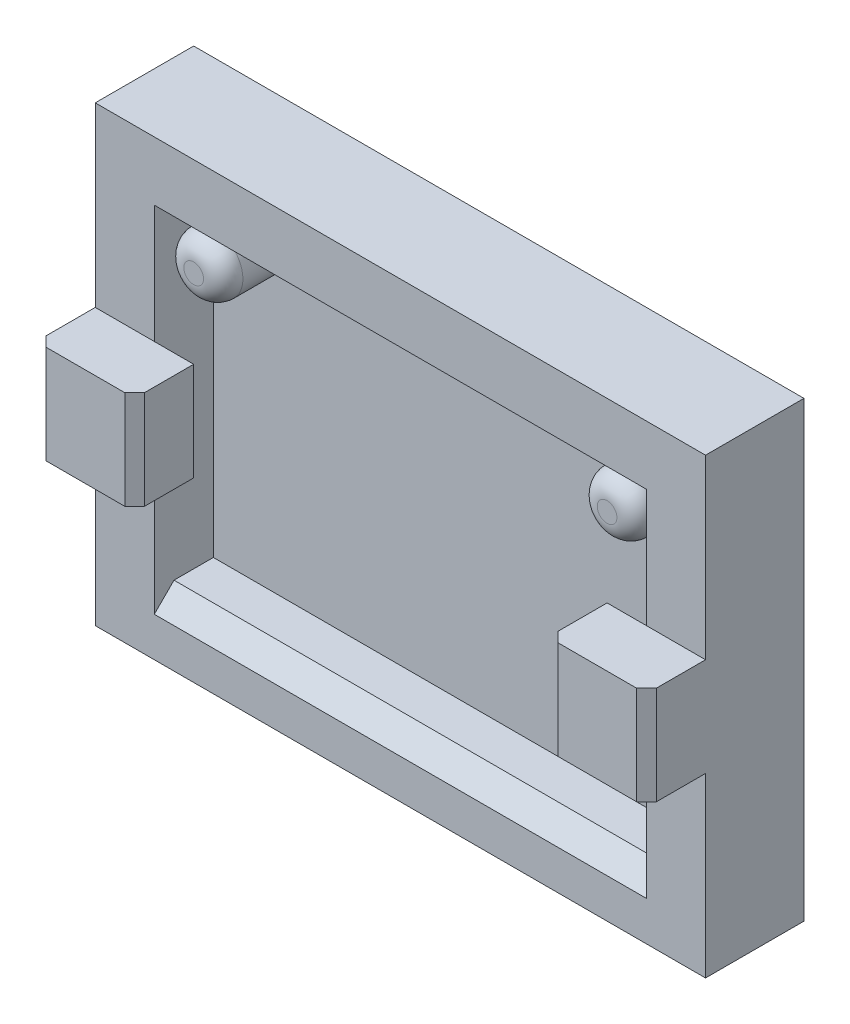
SolidWorks part; units mm, degrees
ref_plane "Plan de face" through (0, 0, 0) normal (0, 0, 1) x (1, 0, 0)
ref_plane "Plan de dessus" through (0, 0, 0) normal (0, 1, 0) x (1, 0, 0)
ref_plane "Plan de droite" through (0, 0, 0) normal (1, 0, 0) x (0, 0, -1)
sketch "Esquisse1" plane through (0, 0, 0) normal (0, 0, 1) x (1, 0, 0)
  line L1 (-31, 23) -> (0, 23)
  line L2 (-31, 23) -> (-31, 0)
  line L3 (-31, 0) -> (0, 0)
  line L4 (0, 23) -> (0, 0)
  dimension "D1" = 31
  dimension "D2" = 23
extrude "Boss.-Extru.1" add sketch "Esquisse1" along normal blind 5
sketch "Esquisse2" plane through (0, 0, 5) normal (0, 0, 1) x (1, 0, 0)
  line L0 (-31, 23) -> (-31, 0) construction
  line L1 (-28, 20) -> (-3, 20)
  line L2 (-28, 20) -> (-28, 3)
  line L3 (-28, 3) -> (-3, 3)
  line L4 (-3, 20) -> (-3, 3)
  line L5 (0, 23) -> (-31, 23) construction
  dimension "D1" = 25
  dimension "D2" = 17
  dimension "D3" = 3
  dimension "D4" = 3
extrude "Enlèv. mat.-Extru.1" cut sketch "Esquisse2" against normal blind 3
sketch "Esquisse3" plane through (0, 0, 2) normal (0, 0, 1) x (1, 0, 0)
  line L0 (-3, 3) -> (-3, 20) construction
  line L1 (-3, 20) -> (-28, 20) construction
  line L2 (-28, 20) -> (-28, 3) construction
  line L3 (-3, 20) -> (-28, 20) construction
  circle A0 centre (-26, 18) radius 1.5
  circle A1 centre (-5, 18) radius 1.5
  dimension "D1" = 3
  dimension "D2" = 3
  dimension "D3" = 2
  dimension "D4" = 2
  dimension "D5" = 2
  dimension "D6" = 2
extrude "Boss.-Extru.2" add sketch "Esquisse3" along normal blind 3
fillet "Congé1" radius 1 2 edges at (-3.5, 18, 5) (-24.5, 18, 5)
sketch "Esquisse4" plane through (0, 0, 5) normal (0, 0, 1) x (1, 0, 0)
  line L0 (-28, 3) -> (-3, 3) construction
  line L1 (-31, 14) -> (-26, 14)
  line L2 (-31, 14) -> (-31, 9)
  line L3 (-31, 9) -> (-26, 9)
  line L4 (-26, 14) -> (-26, 9)
  line L5 (-5, 14) -> (0, 14)
  line L6 (-5, 14) -> (-5, 9)
  line L7 (-5, 9) -> (0, 9)
  line L8 (0, 14) -> (0, 9)
  line L9 (-28, 20) -> (-28, 3) construction
  line L10 (-3, 3) -> (-3, 20) construction
  line L11 (-31, 23) -> (-31, 0) construction
  line L12 (0, 0) -> (0, 23) construction
  dimension "D1" = 5
  dimension "D2" = 5
  dimension "D3" = 6
  dimension "D4" = 6
  dimension "D5" = 2
  dimension "D6" = 2
extrude "Boss.-Extru.3" add sketch "Esquisse4" along normal blind 3
chamfer "Chanfrein1" distance 0.5 angle 45 4 edges at (0, 11.5, 8) (-5, 11.5, 8) (-26, 11.5, 8) (-31, 11.5, 8)
chamfer "Chanfrein2" distance 1 angle 45 1 edges at (-15.5, 3, 5)
